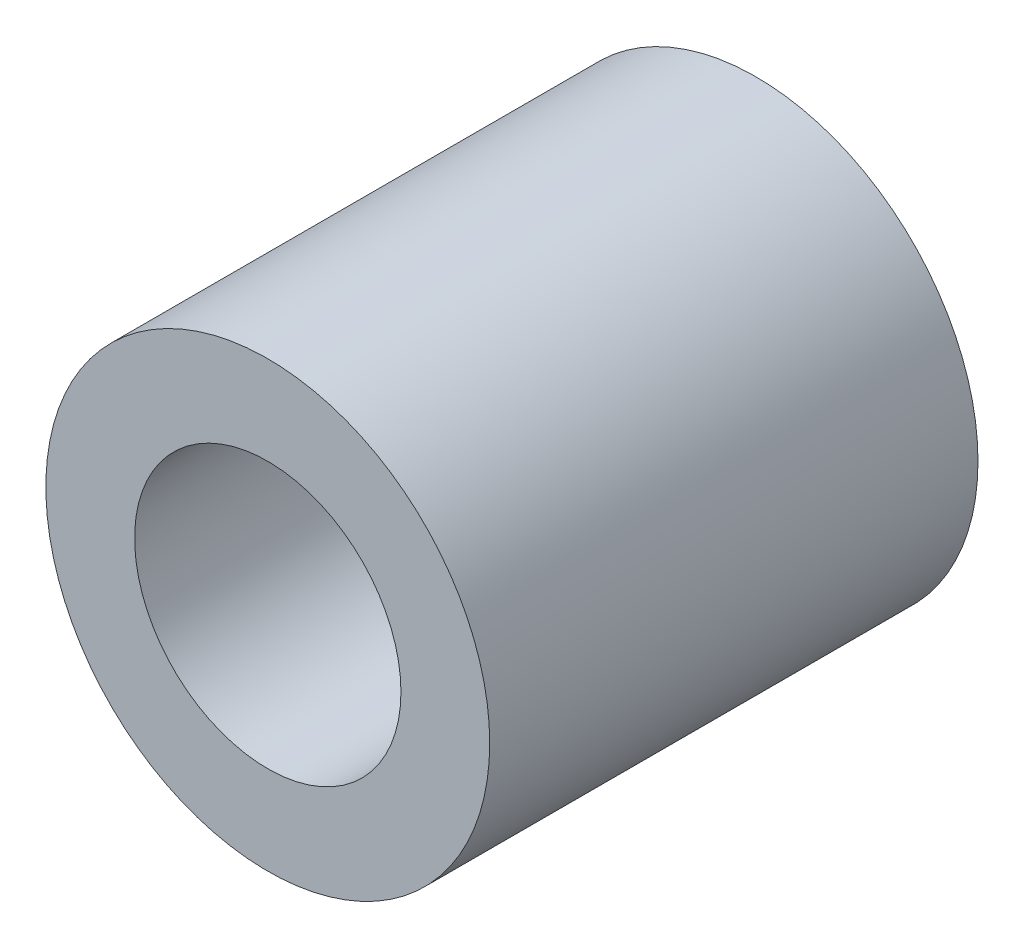
SolidWorks part; units mm, degrees
material "ﾎﾟﾘｵｷｼﾒﾁﾚﾝ(POM)ｱｾﾀｰﾙ共重合体"
ref_plane "Front Plane" through (0, 0, 0) normal (0, 0, 1) x (1, 0, 0)
ref_plane "Top Plane" through (0, 0, 0) normal (0, 1, 0) x (1, 0, 0)
ref_plane "Right Plane" through (0, 0, 0) normal (1, 0, 0) x (0, 0, -1)
sketch "Sketch2" plane through (0, 0, 0) normal (0, 0, 1) x (1, 0, 0)
  circle A0 centre (0, 0) radius 2.5
  circle A1 centre (0, 0) radius 1.5
  dimension "D1" = 3
  dimension "D2" = 5
  dimension "D3" = 5
extrude "Boss-Extrude1" add sketch "Sketch2" along normal blind 5.5
